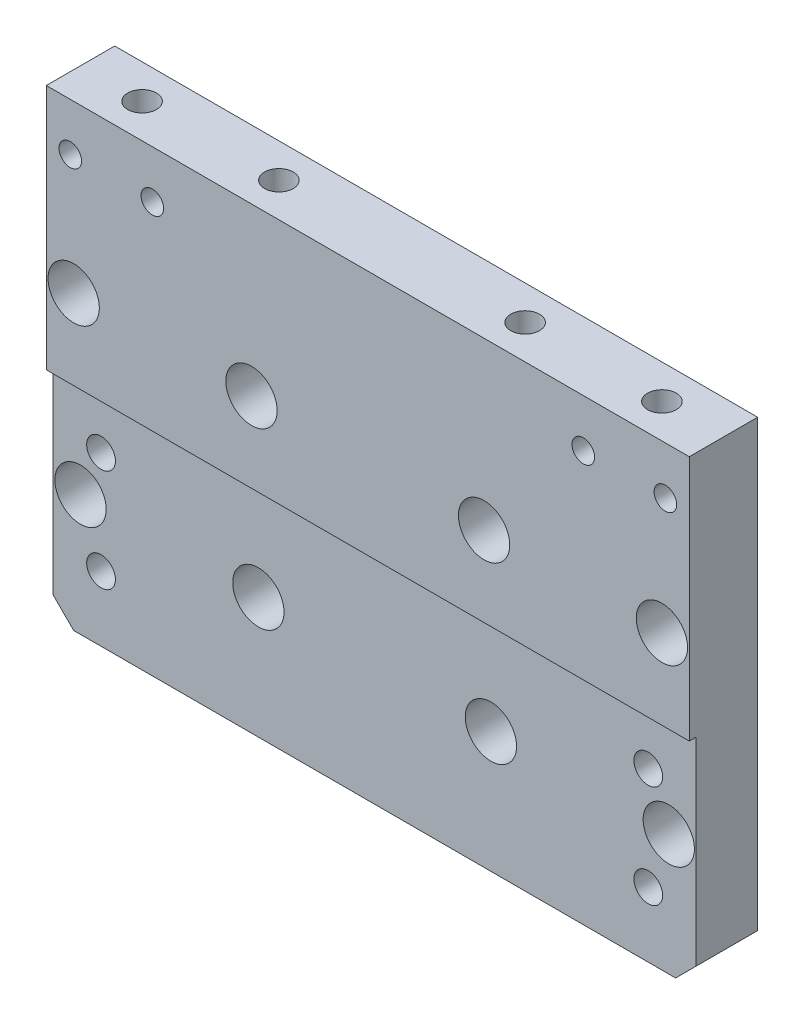
SolidWorks part; units mm, degrees
ref_plane "Front Plane" through (0, 0, 0) normal (0, 0, 1) x (1, 0, 0)
ref_plane "Top Plane" through (0, 0, 0) normal (0, 1, 0) x (1, 0, 0)
ref_plane "Right Plane" through (0, 0, 0) normal (1, 0, 0) x (0, 0, -1)
sketch "Sketch1" plane through (0, 0, 0) normal (0, 0, 1) x (1, 0, 0)
  line L0 (0, 0) -> (0, 81.5188) construction
  line L1 (0, 0) -> (171.2358, 0) construction
  line L2 (0, 0) -> (0, 68)
  line L3 (0, 68) -> (94, 68)
  line L4 (94, 68) -> (94, 0)
  line L5 (94, 0) -> (0, 0)
  dimension "D1" = 68
  dimension "D2" = 94
extrude "Boss-Extrude1" add sketch "Sketch1" along normal blind 10
sketch "Sketch2" plane through (0, 68, 0) normal (0, 1, 0) x (1, 0, 0)
  line L0 (47, 0) -> (47, -10) construction
  line L1 (94, 0) -> (0, 0) construction
  line L2 (94, -10) -> (0, -10) construction
  line L3 (0, -5) -> (94, -5) construction
  line L4 (0, -10) -> (0, 0) construction
  line L5 (94, -10) -> (94, 0) construction
  circle A0 centre (9, -5) radius 3.442
  circle A1 centre (29, -5) radius 3.442
  circle A2 centre (65, -5) radius 3.442
  circle A3 centre (85, -5) radius 3.442
  dimension "D1" = 18
  dimension "D2" = 20
hole_wizard "M5 Tapped Hole1" positions "3DSketch1" profile "Sketch3" tap size "M5" standard "GB"
sketch3d "3DSketch1"
  point P0 (9, 68, 5)
  point P3 (29, 68, 5)
  point P6 (65, 68, 5)
  point P9 (85, 68, 5)
sketch "Sketch3" plane through (9, 68, 5) normal (1, 0, 0) x (0, 0, 1)
  line L0 (0, 0) -> (0, 15.2618)
  line L1 (0, 15.2618) -> (2.1, 14)
  line L2 (2.1, 14) -> (2.1, 0)
  line L5 (2.1, 0) -> (0, 0)
  line L10 (0, 15.2618) -> (-2.1, 14) construction
  line L11 (0, -6.35) -> (0, 107.95) construction
  dimension "Tap Drill Dia." = 4.2
  dimension "Tap Drill Depth" = 14
  dimension "Drill Angle" = 118
cosmetic thread "Hole Thread1" parameters "D1"=10, "D2"=5
cosmetic thread "Hole Thread2" parameters "D1"=10, "D2"=5
cosmetic thread "Hole Thread3" parameters "D1"=10, "D2"=5
cosmetic thread "Hole Thread4" parameters "D1"=10, "D2"=5
sketch "Sketch4" plane through (0, 0, 10) normal (0, 0, 1) x (1, 0, 0)
  line L0 (0, 0) -> (0, 32)
  line L1 (0, 68) -> (0, 0) construction
  line L2 (0, 32) -> (94, 32)
  line L3 (94, 0) -> (94, 68) construction
  line L4 (94, 32) -> (94, 0)
  line L5 (94, 0) -> (0, 0)
  dimension "D1" = 32
extrude "Cut-Extrude1" cut sketch "Sketch4" against normal blind 1
chamfer "Chamfer1" distance 3 angle 45 2 edges at (0, 0, 4.5) (94, 0, 4.5)
sketch "Sketch12" plane through (0, 0, 9) normal (0, 0, 1) x (1, 0, 0)
  line L0 (0, 17.7) -> (94, 17.7) construction
  line L1 (0, 32) -> (0, 3) construction
  line L2 (94, 3) -> (94, 32) construction
  line L3 (3, 0) -> (91, 0) construction
  circle A0 centre (4, 17.7) radius 3.9008
  circle A1 centre (30, 17.7) radius 3.9008
  circle A2 centre (64, 17.7) radius 3.9008
  circle A3 centre (90, 17.7) radius 3.9008
  dimension "D1" = 4
  dimension "D2" = 26
  dimension "D3" = 34
  dimension "D4" = 26
  dimension "D5" = 17.7
hole_wizard "CBORE for M4 Hex Socket Head Cap Screw5" positions "3DSketch6" profile "Sketch13" counterbore size "M4" standard "ISO" end condition through all
sketch3d "3DSketch6"
  point P0 (4, 17.7, 9)
  point P3 (30, 17.7, 9)
  point P6 (64, 17.7, 9)
  point P9 (90, 17.7, 9)
sketch "Sketch13" plane through (4, 17.7, 9) normal (1, 0, 0) x (0, -1, 0)
  line L0 (0, 0) -> (0, 9)
  line L1 (0, 9) -> (2.25, 9)
  line L3 (2.25, 9) -> (2.25, 5.8)
  line L4 (2.25, 5.8) -> (3.75, 5.8)
  line L5 (3.75, 5.8) -> (3.75, 0)
  line L7 (3.75, 0) -> (0, 0)
  line L11 (0, -6.35) -> (0, 107.95) construction
  dimension "Thru Hole Dia." = 4.5
  dimension "Thru Hole Depth" = 9
  dimension "C'Bore Dia." = 7.5
  dimension "C'Bore Depth" = 5.8
sketch "Sketch14" plane through (0, 0, 9) normal (0, 0, 1) x (1, 0, 0)
  line L0 (47, 0) -> (47, 68) construction
  line L1 (3, 0) -> (91, 0) construction
  line L2 (94, 68) -> (0, 68) construction
  line L3 (7, 24.5) -> (7, 9.5) construction
  line L4 (94, 32) -> (0, 32) construction
  circle A0 centre (7, 24.5) radius 1.5
  circle A1 centre (7, 9.5) radius 1.5
  circle A2 centre (87, 9.5) radius 1.5
  circle A3 centre (87, 24.5) radius 1.5
  dimension "D4" = 3
  dimension "D1" = 40
  dimension "D2" = 15
  dimension "D3" = 7.5
hole_wizard "M5 Tapped Hole2" positions "3DSketch7" profile "Sketch15" tap size "M5" standard "GB"
sketch3d "3DSketch7"
  point P0 (7, 24.5, 9)
  point P3 (7, 9.5, 9)
  point P6 (87, 24.5, 9)
  point P9 (87, 9.5, 9)
sketch "Sketch15" plane through (7, 24.5, 9) normal (1, 0, 0) x (0, -1, 0)
  line L0 (0, 0) -> (0, 15.2618)
  line L1 (0, 15.2618) -> (2.1, 14)
  line L2 (2.1, 14) -> (2.1, 0)
  line L5 (2.1, 0) -> (0, 0)
  line L10 (0, 15.2618) -> (-2.1, 14) construction
  line L11 (0, -6.35) -> (0, 107.95) construction
  dimension "Tap Drill Dia." = 4.2
  dimension "Tap Drill Depth" = 14
  dimension "Drill Angle" = 118
cosmetic thread "Hole Thread5" parameters "D1"=9, "D2"=5
cosmetic thread "Hole Thread6" parameters "D1"=9, "D2"=5
cosmetic thread "Hole Thread7" parameters "D1"=9, "D2"=5
cosmetic thread "Hole Thread8" parameters "D1"=9, "D2"=5
sketch "Sketch16" plane through (0, 0, 10) normal (0, 0, 1) x (1, 0, 0)
  line L0 (0, 61) -> (94, 61) construction
  line L1 (0, 68) -> (0, 32) construction
  line L2 (94, 32) -> (94, 68) construction
  line L3 (94, 68) -> (0, 68) construction
  line L4 (47, 68) -> (47, 33.4476) construction
  circle A0 centre (3.5, 61) radius 1.5
  circle A1 centre (15.5, 61) radius 1.5
  circle A2 centre (78.5, 61) radius 1.5
  circle A3 centre (90.5, 61) radius 1.5
  dimension "D4" = 3
  dimension "D1" = 7
  dimension "D2" = 12
  dimension "D3" = 3.5
hole_wizard "M4 Tapped Hole1" positions "3DSketch8" profile "Sketch17" tap size "M4" standard "GB"
sketch3d "3DSketch8"
  point P0 (3.5, 61, 10)
  point P3 (15.5, 61, 10)
  point P6 (78.5, 61, 10)
  point P9 (90.5, 61, 10)
sketch "Sketch17" plane through (3.5, 61, 10) normal (1, 0, 0) x (0, -1, 0)
  line L0 (0, 0) -> (0, 12.4914)
  line L1 (0, 12.4914) -> (1.65, 11.5)
  line L2 (1.65, 11.5) -> (1.65, 0)
  line L5 (1.65, 0) -> (0, 0)
  line L10 (0, 12.4914) -> (-1.65, 11.5) construction
  line L11 (0, -6.35) -> (0, 107.95) construction
  dimension "Tap Drill Dia." = 3.3
  dimension "Tap Drill Depth" = 11.5
  dimension "Drill Angle" = 118
cosmetic thread "Hole Thread9" parameters "D1"=8, "D2"=4
cosmetic thread "Hole Thread10" parameters "D1"=8, "D2"=4
cosmetic thread "Hole Thread11" parameters "D1"=8, "D2"=4
cosmetic thread "Hole Thread12" parameters "D1"=8, "D2"=4
sketch "Sketch18" plane through (0, 0, 10) normal (0, 0, 1) x (1, 0, 0)
  line L0 (47, 68) -> (47, 0) construction
  line L1 (94, 68) -> (0, 68) construction
  line L2 (3, 0) -> (91, 0) construction
  line L3 (0, 43.7) -> (94, 43.7) construction
  line L4 (0, 68) -> (0, 32) construction
  line L5 (94, 32) -> (94, 68) construction
  line L6 (0, 17.7) -> (94, 17.7) construction
  circle A1 centre (4, 43.7) radius 3
  circle A2 centre (30, 43.7) radius 3
  circle A3 centre (64, 43.7) radius 3
  circle A4 centre (90, 43.7) radius 3
  dimension "D2" = 6
  dimension "D1" = 26
  dimension "D3" = 26
  dimension "D4" = 4
hole_wizard "CBORE for M4 Hex Socket Head Cap Screw6" positions "3DSketch9" profile "Sketch19" counterbore size "M4" standard "ISO" end condition through all
sketch3d "3DSketch9"
  point P0 (4, 43.7, 10)
  point P3 (30, 43.7, 10)
  point P6 (64, 43.7, 10)
  point P9 (90, 43.7, 10)
sketch "Sketch19" plane through (4, 43.7, 10) normal (1, 0, 0) x (0, -1, 0)
  line L0 (0, 0) -> (0, 10)
  line L1 (0, 10) -> (2.25, 10)
  line L3 (2.25, 10) -> (2.25, 5.8)
  line L4 (2.25, 5.8) -> (3.75, 5.8)
  line L5 (3.75, 5.8) -> (3.75, 0)
  line L7 (3.75, 0) -> (0, 0)
  line L11 (0, -6.35) -> (0, 107.95) construction
  dimension "Thru Hole Dia." = 4.5
  dimension "Thru Hole Depth" = 10
  dimension "C'Bore Dia." = 7.5
  dimension "C'Bore Depth" = 5.8
